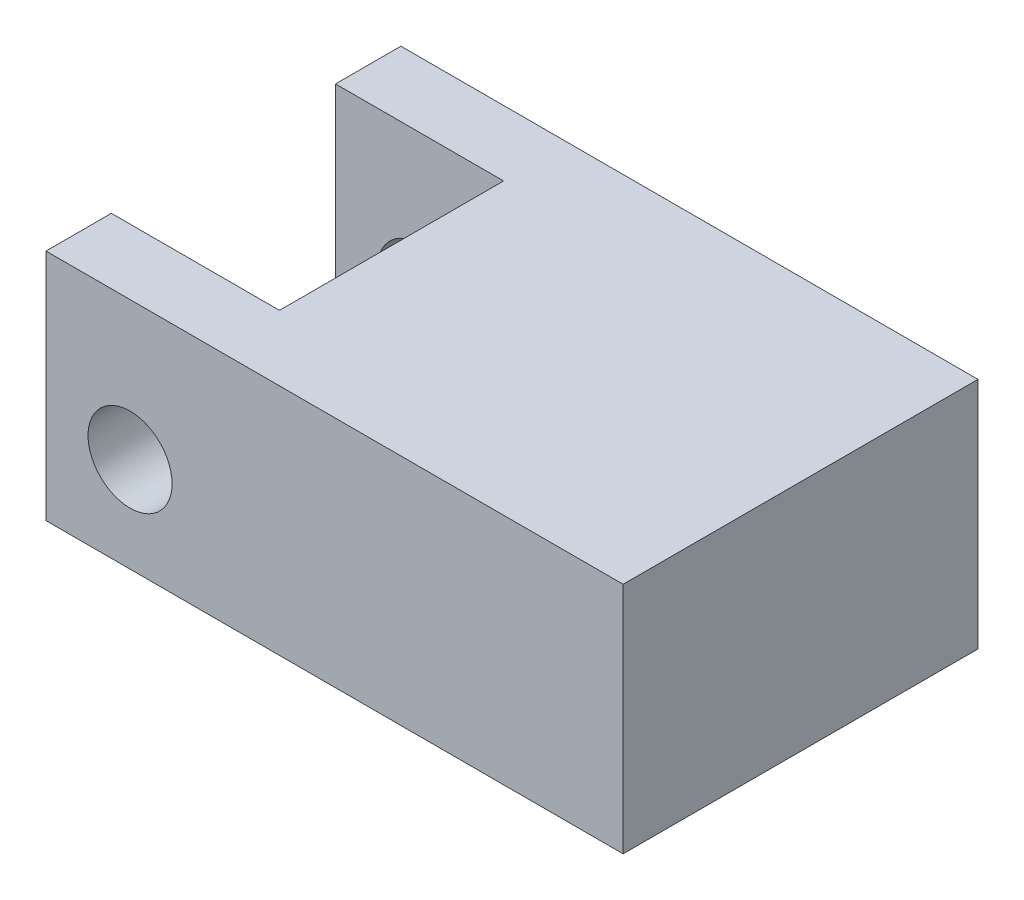
SolidWorks part; units mm, degrees
ref_plane "Front Plane" through (0, 0, 0) normal (0, 0, 1) x (1, 0, 0)
ref_plane "Top Plane" through (0, 0, 0) normal (0, 1, 0) x (1, 0, 0)
ref_plane "Right Plane" through (0, 0, 0) normal (1, 0, 0) x (0, 0, -1)
sketch "Sketch1" plane through (0, 0, 0) normal (0, 0, 1) x (1, 0, 0)
  line L1 (-15.45, 6.25) -> (15.45, 6.25)
  line L2 (-15.45, 6.25) -> (-15.45, -6.25)
  line L3 (-15.45, -6.25) -> (15.45, -6.25)
  line L4 (15.45, 6.25) -> (15.45, -6.25)
  line L5 (-15.45, 6.25) -> (15.45, -6.25) construction
  line L6 (-15.45, -6.25) -> (15.45, 6.25) construction
  point P0 (0, 0)
  dimension "D1" = 30.9
  dimension "D2" = 12.5
extrude "Boss-Extrude1" add sketch "Sketch1" along normal mid plane 19
sketch "Sketch2" plane through (0, 6.25, 0) normal (0, 1, 0) x (1, 0, 0)
  line L0 (-15.45, 6) -> (-6.45, 6)
  line L1 (-15.45, -9.5) -> (-15.45, 9.5) construction
  line L2 (-6.45, 6) -> (-6.45, -6)
  line L3 (-6.45, -6) -> (-15.45, -6)
  line L4 (-15.45, -6) -> (-15.45, 6)
  point P4 (-15.45, 0)
  dimension "D1" = 12
  dimension "D2" = 9
extrude "Cut-Extrude1" cut sketch "Sketch2" against normal up to surface (12.5 mm away) up to face at (0, -6.25, 0)
sketch "Sketch3" plane through (0, 0, 9.5) normal (0, 0, 1) x (1, 0, 0)
  line L1 (-15.45, 6.25) -> (-15.45, -6.25) construction
  line L2 (-15.45, -6.25) -> (15.45, -6.25) construction
  circle A0 centre (-10.95, -1.17) radius 2.25
  dimension "D1" = 4.5
  dimension "D2" = 4.5
  dimension "D3" = 5.08
extrude "Cut-Extrude2" cut sketch "Sketch3" against normal up to surface (19 mm away) up to face at (0, 0, -9.5)
